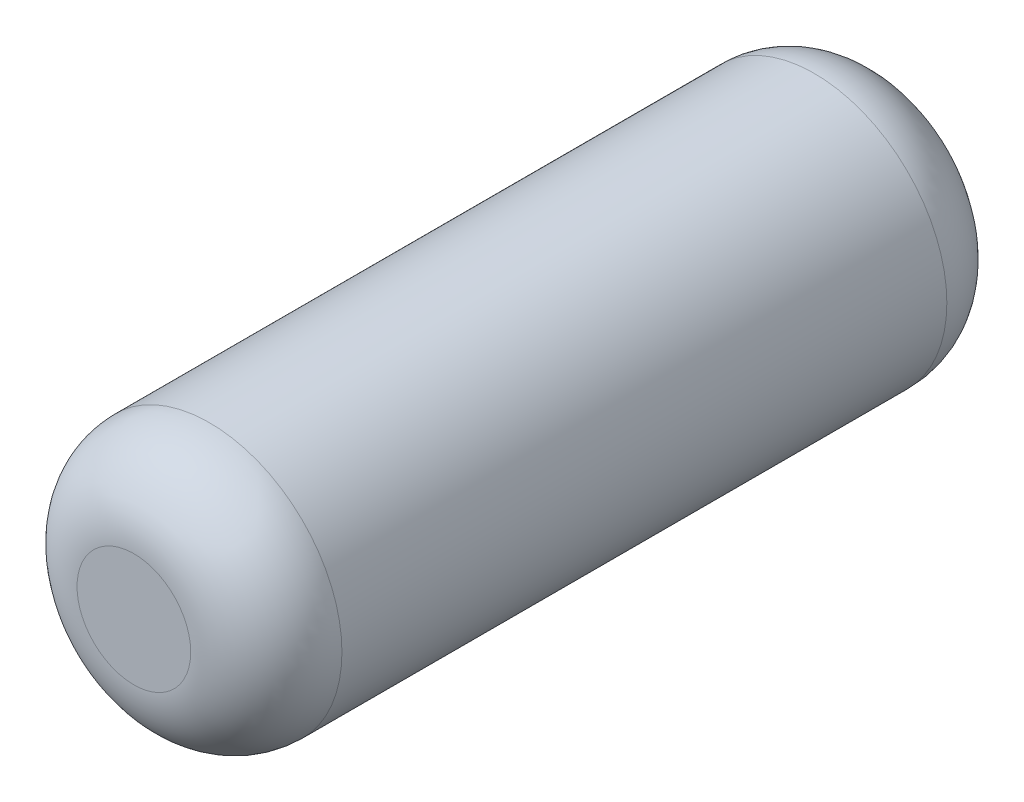
SolidWorks part; units mm, degrees
ref_plane "Front" through (0, 0, 0) normal (0, 0, 1) x (1, 0, 0)
ref_plane "Top" through (0, 0, 0) normal (0, 1, 0) x (1, 0, 0)
ref_plane "Right" through (0, 0, 0) normal (1, 0, 0) x (0, 0, -1)
sketch "Sketch1" plane through (0, 0, 0) normal (0, 0, 1) x (1, 0, 0)
  circle A0 centre (0, 0) radius 44.4904
  dimension "D1" = 88.9809
extrude "Extrude1" add sketch "Sketch1" along normal blind 254
sketch "Sketch2" plane through (0, 0, 254) normal (0, 0, 1) x (1, 0, 0)
  point P0 (0, 0)
fillet "Fillet1" radius 25.4 2 edges at (44.4904, 0, 0) (44.4904, 0, 254)
